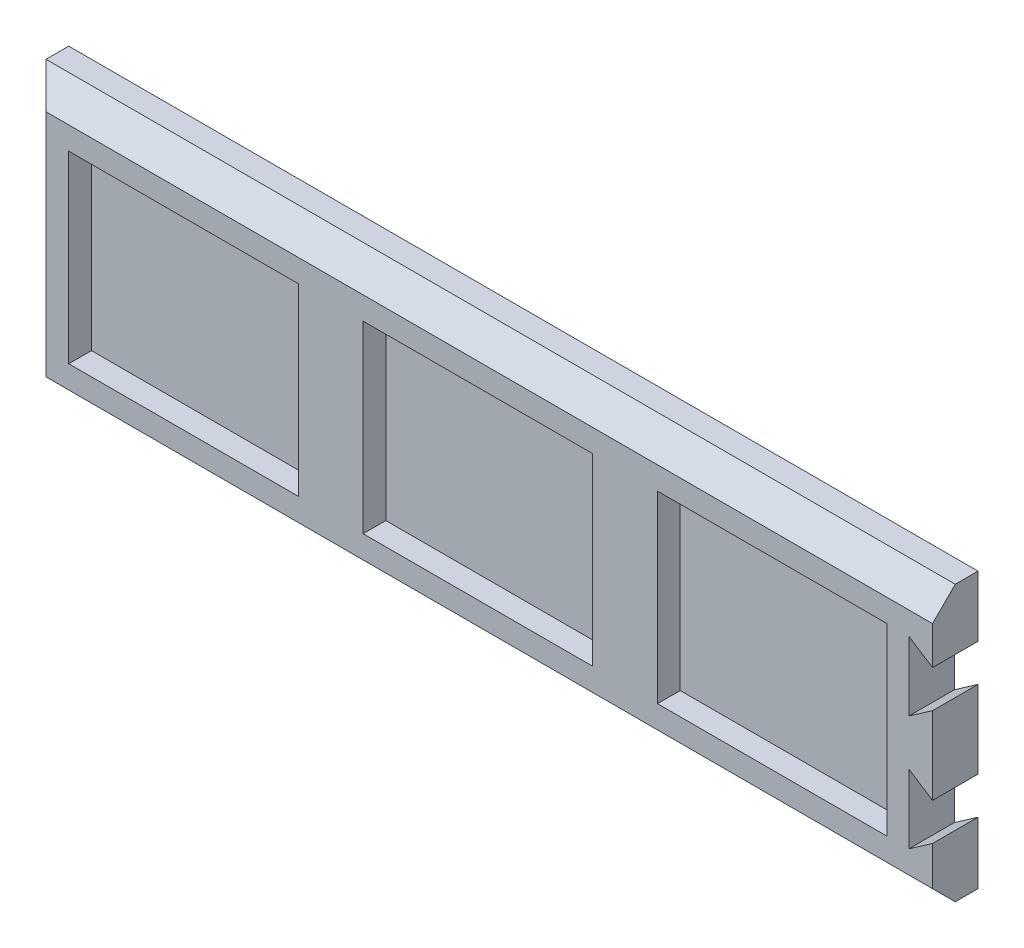
SolidWorks part; units mm, degrees
ref_plane "Ebene vorne" through (0, 0, 0) normal (0, 0, 1) x (1, 0, 0)
ref_plane "Ebene oben" through (0, 0, 0) normal (0, 1, 0) x (1, 0, 0)
ref_plane "Ebene rechts" through (0, 0, 0) normal (1, 0, 0) x (0, 0, -1)
sketch "Skizze1" plane through (0, 0, 0) normal (0, 0, 1) x (1, 0, 0)
  line L0 (-8.0717, 0) -> (126.7564, 0) construction
  line L1 (0, 30.25) -> (200, 30.25)
  line L2 (0, 30.25) -> (0, -30.25)
  line L3 (0, -30.25) -> (200, -30.25)
  line L4 (200, 30.25) -> (200, -30.25)
  dimension "D1" = 60.5
  dimension "200" = 200
extrude "Aufsatz-Linear austragen1" add sketch "Skizze1" along normal blind 10
sketch "Skizze2" plane through (0, 0, 10) normal (0, 0, 1) x (1, 0, 0)
  line L0 (0, 30.25) -> (0, -30.25) construction
  line L1 (10, 20.25) -> (60.5, 20.25)
  line L2 (10, 20.25) -> (10, -20.25)
  line L3 (10, -20.25) -> (60.5, -20.25)
  line L4 (60.5, 20.25) -> (60.5, -20.25)
  line L5 (-18.0232, 0) -> (204.1757, 0) construction
  line L6 (74.75, 20.25) -> (74.75, -20.25)
  line L7 (74.75, 20.25) -> (125.25, 20.25)
  line L8 (125.25, 20.25) -> (125.25, -20.25)
  line L9 (74.75, -20.25) -> (125.25, -20.25)
  line L10 (139.5, 20.25) -> (139.5, -20.25)
  line L11 (139.5, 20.25) -> (190, 20.25)
  line L12 (190, 20.25) -> (190, -20.25)
  line L13 (139.5, -20.25) -> (190, -20.25)
  line L14 (200, -30.25) -> (200, 30.25) construction
  dimension "D1" = 50.5
  dimension "D2" = 40.5
  dimension "D3" = 10
  dimension "D5" = 10
  dimension "D4" = 3
extrude "Schnitt-Linear austragen1" cut sketch "Skizze2" against normal blind 5
chamfer "Fase1" distance 5 angle 45 3 edges at (100, -30.25, 10) (100, 30.25, 10) (0, 0, 10)
sketch "Skizze3" plane through (0, 0, 10) normal (0, 0, 1) x (1, 0, 0)
  line L14 (-9.8291, 0) -> (248.2195, 0) construction
sketch "Skizze4" plane through (0, 0, 10) normal (0, 0, 1) x (1, 0, 0)
  line L0 (200, 16.8736) -> (194.8, 20.25)
  line L1 (200, -25.25) -> (200, 25.25) construction
  line L2 (194.8, 20.25) -> (194.8, 5.05)
  line L3 (194.8, 5.05) -> (200, 8.6736)
  line L4 (200, 8.6736) -> (200, 16.8736)
  line L5 (200, -8.4264) -> (194.8, -5.05)
  line L6 (194.8, -5.05) -> (194.8, -20.25)
  line L7 (194.8, -20.25) -> (200, -16.6264)
  line L8 (200, -16.6264) -> (200, -8.4264)
  line L10 (0, 30.25) -> (200, 30.25) construction
  line L11 (200, -30.25) -> (0, -30.25) construction
  dimension "D1" = 8.2
  dimension "D2" = 15.2
  dimension "D3" = 8.2
  dimension "D4" = 15.2
  dimension "D5" = 5.2
  dimension "D6" = 10
  dimension "D7" = 10
extrude "Schnitt-Linear austragen2" cut sketch "Skizze4" against normal blind 10
